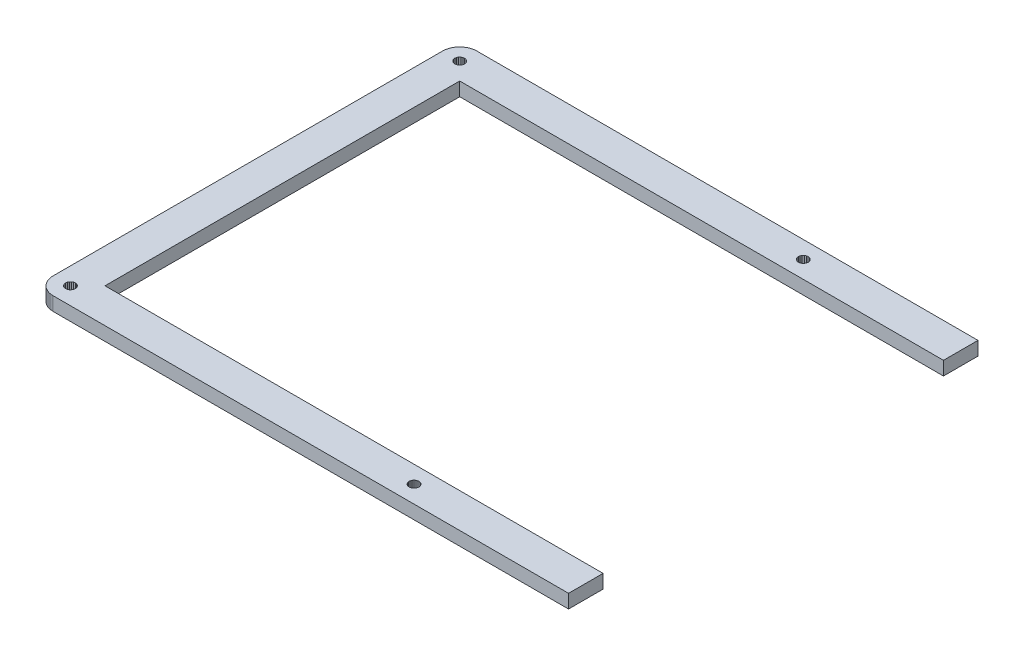
SolidWorks part; units mm, degrees
material "Copper"
ref_plane "Front Plane" through (0, 0, 0) normal (0, 0, 1) x (1, 0, 0)
ref_plane "Top Plane" through (0, 0, 0) normal (0, 1, 0) x (1, 0, 0)
ref_plane "Right Plane" through (0, 0, 0) normal (1, 0, 0) x (0, 0, -1)
sketch "Sketch1" plane through (0, 0, 0) normal (0, 1, 0) x (1, 0, 0)
  line L0 (365.806, 147.967) -> (366.279, 147.949)
  line L1 (366.279, 147.949) -> (366.748, 147.894)
  line L2 (366.748, 147.894) -> (367.21, 147.803)
  line L3 (367.21, 147.803) -> (367.661, 147.675)
  line L4 (367.661, 147.675) -> (368.106, 147.511)
  line L5 (368.106, 147.511) -> (368.533, 147.314)
  line L6 (368.533, 147.314) -> (368.942, 147.085)
  line L7 (368.942, 147.085) -> (369.334, 146.822)
  line L8 (369.334, 146.822) -> (369.704, 146.529)
  line L9 (369.704, 146.529) -> (370.05, 146.21)
  line L10 (370.05, 146.21) -> (370.371, 145.865)
  line L11 (370.371, 145.865) -> (370.664, 145.495)
  line L12 (370.664, 145.495) -> (370.925, 145.102)
  line L13 (370.925, 145.102) -> (371.154, 144.691)
  line L14 (371.154, 144.691) -> (371.352, 144.264)
  line L15 (371.352, 144.264) -> (371.514, 143.822)
  line L16 (371.514, 143.822) -> (371.641, 143.368)
  line L17 (371.641, 143.368) -> (371.733, 142.907)
  line L18 (371.733, 142.907) -> (371.789, 142.44)
  line L19 (371.789, 142.44) -> (371.807, 141.967)
  line L20 (371.807, 141.967) -> (371.807, 6.0909)
  line L21 (371.807, 6.0909) -> (371.789, 5.621)
  line L22 (371.789, 5.621) -> (371.733, 5.1539)
  line L23 (371.733, 5.1539) -> (371.641, 4.6909)
  line L24 (371.641, 4.6909) -> (371.514, 4.2375)
  line L25 (371.514, 4.2375) -> (371.352, 3.7951)
  line L26 (371.352, 3.7951) -> (371.154, 3.3679)
  line L27 (371.154, 3.3679) -> (370.925, 2.9573)
  line L28 (370.925, 2.9573) -> (370.664, 2.5645)
  line L29 (370.664, 2.5645) -> (370.371, 2.1966)
  line L30 (370.371, 2.1966) -> (370.05, 1.8493)
  line L31 (370.05, 1.8493) -> (369.704, 1.5296)
  line L32 (369.704, 1.5296) -> (369.334, 1.2375)
  line L33 (369.334, 1.2375) -> (368.942, 0.9757)
  line L34 (368.942, 0.9757) -> (368.533, 0.7455)
  line L35 (368.533, 0.7455) -> (368.106, 0.5498)
  line L36 (368.106, 0.5498) -> (367.661, 0.3859)
  line L37 (367.661, 0.3859) -> (367.21, 0.2577)
  line L38 (367.21, 0.2577) -> (366.748, 0.1654)
  line L39 (366.748, 0.1654) -> (366.279, 0.1102)
  line L40 (366.279, 0.1102) -> (365.806, 0.091)
  line L41 (365.806, 0.091) -> (6.095, 0.091)
  line L42 (6.095, 0.091) -> (5.6238, 0.1102)
  line L43 (5.6238, 0.1102) -> (5.1553, 0.1654)
  line L44 (5.1553, 0.1654) -> (4.6936, 0.2577)
  line L45 (4.6936, 0.2577) -> (4.2402, 0.3859)
  line L46 (4.2402, 0.3859) -> (3.7979, 0.5498)
  line L47 (3.7979, 0.5498) -> (3.3707, 0.7455)
  line L48 (3.3707, 0.7455) -> (2.96, 0.9757)
  line L49 (2.96, 0.9757) -> (2.5673, 1.2375)
  line L50 (2.5673, 1.2375) -> (2.198, 1.5296)
  line L51 (2.198, 1.5296) -> (1.8521, 1.8493)
  line L52 (1.8521, 1.8493) -> (1.5324, 2.1966)
  line L53 (1.5324, 2.1966) -> (1.2402, 2.5645)
  line L54 (1.2402, 2.5645) -> (0.9784, 2.9573)
  line L55 (0.9784, 2.9573) -> (0.7483, 3.3679)
  line L56 (0.7483, 3.3679) -> (0.5512, 3.7951)
  line L57 (0.5512, 3.7951) -> (0.3872, 4.2375)
  line L58 (0.3872, 4.2375) -> (0.2591, 4.6909)
  line L59 (0.2591, 4.6909) -> (0.1681, 5.1539)
  line L60 (0.1681, 5.1539) -> (0.113, 5.621)
  line L61 (0.113, 5.621) -> (0.0937, 6.0923)
  line L62 (0.0937, 6.0923) -> (0.0951, 141.967)
  line L63 (0.0951, 141.967) -> (0.113, 142.44)
  line L64 (0.113, 142.44) -> (0.1681, 142.907)
  line L65 (0.1681, 142.907) -> (0.2591, 143.368)
  line L66 (0.2591, 143.368) -> (0.3872, 143.822)
  line L67 (0.3872, 143.822) -> (0.5512, 144.264)
  line L68 (0.5512, 144.264) -> (0.7483, 144.691)
  line L69 (0.7483, 144.691) -> (0.9784, 145.102)
  line L70 (0.9784, 145.102) -> (1.2402, 145.495)
  line L71 (1.2402, 145.495) -> (1.5324, 145.865)
  line L72 (1.5324, 145.865) -> (1.8521, 146.21)
  line L73 (1.8521, 146.21) -> (2.198, 146.529)
  line L74 (2.198, 146.529) -> (2.5673, 146.822)
  line L75 (2.5673, 146.822) -> (2.96, 147.085)
  line L76 (2.96, 147.085) -> (3.3707, 147.314)
  line L77 (3.3707, 147.314) -> (3.7979, 147.511)
  line L78 (3.7979, 147.511) -> (4.2402, 147.675)
  line L79 (4.2402, 147.675) -> (4.6936, 147.803)
  line L80 (4.6936, 147.803) -> (5.1553, 147.894)
  line L81 (5.1553, 147.894) -> (5.6238, 147.949)
  line L82 (5.6238, 147.949) -> (6.095, 147.968)
  line L83 (6.095, 147.968) -> (365.806, 147.967)
  line L84 (365.252, 7.757) -> (364.769, 7.5117)
  line L85 (364.769, 7.5117) -> (364.388, 7.13)
  line L86 (364.388, 7.13) -> (364.141, 6.6504)
  line L87 (364.141, 6.6504) -> (364.06, 6.1157)
  line L88 (364.06, 6.1157) -> (364.141, 5.5838)
  line L89 (364.141, 5.5838) -> (364.388, 5.1029)
  line L90 (364.388, 5.1029) -> (364.769, 4.7211)
  line L91 (364.769, 4.7211) -> (365.252, 4.4759)
  line L92 (365.252, 4.4759) -> (365.781, 4.3918)
  line L93 (365.781, 4.3918) -> (366.317, 4.4759)
  line L94 (366.317, 4.4759) -> (366.797, 4.7211)
  line L95 (366.797, 4.7211) -> (367.178, 5.1029)
  line L96 (367.178, 5.1029) -> (367.425, 5.5838)
  line L97 (367.425, 5.5838) -> (367.506, 6.1157)
  line L98 (367.506, 6.1157) -> (367.425, 6.6504)
  line L99 (367.425, 6.6504) -> (367.178, 7.13)
  line L100 (367.178, 7.13) -> (366.797, 7.5117)
  line L101 (366.797, 7.5117) -> (366.317, 7.757)
  line L102 (366.317, 7.757) -> (365.781, 7.8411)
  line L103 (365.781, 7.8411) -> (365.252, 7.757)
  line L104 (245.361, 7.757) -> (244.88, 7.5117)
  line L105 (244.88, 7.5117) -> (244.5, 7.13)
  line L106 (244.5, 7.13) -> (244.255, 6.6504)
  line L107 (244.255, 6.6504) -> (244.169, 6.1157)
  line L108 (244.169, 6.1157) -> (244.255, 5.5838)
  line L109 (244.255, 5.5838) -> (244.5, 5.1029)
  line L110 (244.5, 5.1029) -> (244.88, 4.7211)
  line L111 (244.88, 4.7211) -> (245.361, 4.4759)
  line L112 (245.361, 4.4759) -> (245.894, 4.3918)
  line L113 (245.894, 4.3918) -> (246.428, 4.4759)
  line L114 (246.428, 4.4759) -> (246.908, 4.7211)
  line L115 (246.908, 4.7211) -> (247.29, 5.1029)
  line L116 (247.29, 5.1029) -> (247.536, 5.5838)
  line L117 (247.536, 5.5838) -> (247.62, 6.1157)
  line L118 (247.62, 6.1157) -> (247.536, 6.6504)
  line L119 (247.536, 6.6504) -> (247.29, 7.13)
  line L120 (247.29, 7.13) -> (246.908, 7.5117)
  line L121 (246.908, 7.5117) -> (246.428, 7.757)
  line L122 (246.428, 7.757) -> (245.894, 7.8411)
  line L123 (245.894, 7.8411) -> (245.361, 7.757)
  line L124 (125.473, 7.757) -> (124.992, 7.5117)
  line L125 (124.992, 7.5117) -> (124.612, 7.13)
  line L126 (124.612, 7.13) -> (124.365, 6.6504)
  line L127 (124.365, 6.6504) -> (124.281, 6.1157)
  line L128 (124.281, 6.1157) -> (124.365, 5.5838)
  line L129 (124.365, 5.5838) -> (124.612, 5.1029)
  line L130 (124.612, 5.1029) -> (124.992, 4.7211)
  line L131 (124.992, 4.7211) -> (125.473, 4.4759)
  line L132 (125.473, 4.4759) -> (126.007, 4.3918)
  line L133 (126.007, 4.3918) -> (126.54, 4.4759)
  line L134 (126.54, 4.4759) -> (127.021, 4.7211)
  line L135 (127.021, 4.7211) -> (127.403, 5.1029)
  line L136 (127.403, 5.1029) -> (127.648, 5.5838)
  line L137 (127.648, 5.5838) -> (127.732, 6.1157)
  line L138 (127.732, 6.1157) -> (127.648, 6.6504)
  line L139 (127.648, 6.6504) -> (127.403, 7.13)
  line L140 (127.403, 7.13) -> (127.021, 7.5117)
  line L141 (127.021, 7.5117) -> (126.54, 7.757)
  line L142 (126.54, 7.757) -> (126.007, 7.8411)
  line L143 (126.007, 7.8411) -> (125.473, 7.757)
  line L144 (5.5852, 7.757) -> (5.1056, 7.5117)
  line L145 (5.1056, 7.5117) -> (4.7239, 7.13)
  line L146 (4.7239, 7.13) -> (4.4786, 6.6504)
  line L147 (4.4786, 6.6504) -> (4.3932, 6.1157)
  line L148 (4.3932, 6.1157) -> (4.4786, 5.5838)
  line L149 (4.4786, 5.5838) -> (4.7239, 5.1029)
  line L150 (4.7239, 5.1029) -> (5.1056, 4.7211)
  line L151 (5.1056, 4.7211) -> (5.5852, 4.4759)
  line L152 (5.5852, 4.4759) -> (6.1185, 4.3918)
  line L153 (6.1185, 4.3918) -> (6.6532, 4.4759)
  line L154 (6.6532, 4.4759) -> (7.1327, 4.7211)
  line L155 (7.1327, 4.7211) -> (7.5145, 5.1029)
  line L156 (7.5145, 5.1029) -> (7.7597, 5.5838)
  line L157 (7.7597, 5.5838) -> (7.8438, 6.1157)
  line L158 (7.8438, 6.1157) -> (7.7597, 6.6504)
  line L159 (7.7597, 6.6504) -> (7.5145, 7.13)
  line L160 (7.5145, 7.13) -> (7.1327, 7.5117)
  line L161 (7.1327, 7.5117) -> (6.6532, 7.757)
  line L162 (6.6532, 7.757) -> (6.1185, 7.8411)
  line L163 (6.1185, 7.8411) -> (5.5852, 7.757)
  line L164 (12.1447, 135.919) -> (359.759, 135.919)
  line L165 (359.759, 135.919) -> (359.759, 12.1405)
  line L166 (359.759, 12.1405) -> (12.1447, 12.1405)
  line L167 (12.1447, 12.1405) -> (12.1447, 135.919)
  line L168 (125.473, 143.583) -> (124.992, 143.338)
  line L169 (124.992, 143.338) -> (124.612, 142.956)
  line L170 (124.612, 142.956) -> (124.365, 142.477)
  line L171 (124.365, 142.477) -> (124.281, 141.942)
  line L172 (124.281, 141.942) -> (124.365, 141.409)
  line L173 (124.365, 141.409) -> (124.612, 140.929)
  line L174 (124.612, 140.929) -> (124.992, 140.547)
  line L175 (124.992, 140.547) -> (125.473, 140.302)
  line L176 (125.473, 140.302) -> (126.007, 140.217)
  line L177 (126.007, 140.217) -> (126.54, 140.302)
  line L178 (126.54, 140.302) -> (127.021, 140.547)
  line L179 (127.021, 140.547) -> (127.403, 140.929)
  line L180 (127.403, 140.929) -> (127.648, 141.409)
  line L181 (127.648, 141.409) -> (127.732, 141.942)
  line L182 (127.732, 141.942) -> (127.648, 142.477)
  line L183 (127.648, 142.477) -> (127.403, 142.956)
  line L184 (127.403, 142.956) -> (127.021, 143.338)
  line L185 (127.021, 143.338) -> (126.54, 143.583)
  line L186 (126.54, 143.583) -> (126.007, 143.667)
  line L187 (126.007, 143.667) -> (125.473, 143.583)
  line L188 (245.361, 143.583) -> (244.88, 143.338)
  line L189 (244.88, 143.338) -> (244.5, 142.956)
  line L190 (244.5, 142.956) -> (244.255, 142.477)
  line L191 (244.255, 142.477) -> (244.169, 141.942)
  line L192 (244.169, 141.942) -> (244.255, 141.409)
  line L193 (244.255, 141.409) -> (244.5, 140.929)
  line L194 (244.5, 140.929) -> (244.88, 140.547)
  line L195 (244.88, 140.547) -> (245.361, 140.302)
  line L196 (245.361, 140.302) -> (245.894, 140.217)
  line L197 (245.894, 140.217) -> (246.428, 140.302)
  line L198 (246.428, 140.302) -> (246.908, 140.547)
  line L199 (246.908, 140.547) -> (247.29, 140.929)
  line L200 (247.29, 140.929) -> (247.536, 141.409)
  line L201 (247.536, 141.409) -> (247.62, 141.942)
  line L202 (247.62, 141.942) -> (247.536, 142.477)
  line L203 (247.536, 142.477) -> (247.29, 142.956)
  line L204 (247.29, 142.956) -> (246.908, 143.338)
  line L205 (246.908, 143.338) -> (246.428, 143.583)
  line L206 (246.428, 143.583) -> (245.894, 143.667)
  line L207 (245.894, 143.667) -> (245.361, 143.583)
  line L208 (365.252, 143.583) -> (364.769, 143.338)
  line L209 (364.769, 143.338) -> (364.388, 142.956)
  line L210 (364.388, 142.956) -> (364.141, 142.477)
  line L211 (364.141, 142.477) -> (364.06, 141.942)
  line L212 (364.06, 141.942) -> (364.141, 141.409)
  line L213 (364.141, 141.409) -> (364.388, 140.929)
  line L214 (364.388, 140.929) -> (364.769, 140.547)
  line L215 (364.769, 140.547) -> (365.252, 140.302)
  line L216 (365.252, 140.302) -> (365.781, 140.217)
  line L217 (365.781, 140.217) -> (366.317, 140.302)
  line L218 (366.317, 140.302) -> (366.797, 140.547)
  line L219 (366.797, 140.547) -> (367.178, 140.929)
  line L220 (367.178, 140.929) -> (367.425, 141.409)
  line L221 (367.425, 141.409) -> (367.506, 141.942)
  line L222 (367.506, 141.942) -> (367.425, 142.477)
  line L223 (367.425, 142.477) -> (367.178, 142.956)
  line L224 (367.178, 142.956) -> (366.797, 143.338)
  line L225 (366.797, 143.338) -> (366.317, 143.583)
  line L226 (366.317, 143.583) -> (365.781, 143.667)
  line L227 (365.781, 143.667) -> (365.252, 143.583)
  line L228 (5.5852, 143.583) -> (5.1056, 143.338)
  line L229 (5.1056, 143.338) -> (4.7239, 142.956)
  line L230 (4.7239, 142.956) -> (4.4786, 142.477)
  line L231 (4.4786, 142.477) -> (4.3932, 141.942)
  line L232 (4.3932, 141.942) -> (4.4786, 141.409)
  line L233 (4.4786, 141.409) -> (4.7239, 140.929)
  line L234 (4.7239, 140.929) -> (5.1056, 140.547)
  line L235 (5.1056, 140.547) -> (5.5852, 140.302)
  line L236 (5.5852, 140.302) -> (6.1185, 140.217)
  line L237 (6.1185, 140.217) -> (6.6532, 140.302)
  line L238 (6.6532, 140.302) -> (7.1327, 140.547)
  line L239 (7.1327, 140.547) -> (7.5145, 140.929)
  line L240 (7.5145, 140.929) -> (7.7597, 141.409)
  line L241 (7.7597, 141.409) -> (7.8438, 141.942)
  line L242 (7.8438, 141.942) -> (7.7597, 142.477)
  line L243 (7.7597, 142.477) -> (7.5145, 142.956)
  line L244 (7.5145, 142.956) -> (7.1327, 143.338)
  line L245 (7.1327, 143.338) -> (6.6532, 143.583)
  line L246 (6.6532, 143.583) -> (6.1185, 143.667)
  line L247 (6.1185, 143.667) -> (5.5852, 143.583)
  line L248 (185.9505, 147.9675) -> (185.9505, 0.091)
extrude "Boss-Extrude2" add sketch "Sketch1" along normal blind 4.7625 contours L248 L83 L82 L81 L80 L79 L78 L77 L76 L75 L74 L73 L72 L71 L70 L69 L68 L67 L66 L65 L64 L63 L62 L61 L60 L59 L58 L57 L56 L55 L54 L53 L52 L51 L50 L49 L48 L47 L46 L45 L44 L43 L42 L41 L166 L167 L164 L247 L246
sketch "Sketch2" plane through (0, 4.7625, 0) normal (0, 1, 0) x (1, 0, 0)
  line L1 (185.9505, 147.9675) -> (185.9505, 135.919) construction
  line L2 (12.1447, 135.919) -> (185.9505, 135.919) construction
  line L4 (180.9505, 141.9433) -> (180.9505, 147.9675)
  line L5 (180.9505, 147.9675) -> (185.9505, 147.9675)
  line L6 (185.9505, 141.9433) -> (185.9505, 147.9675)
  line L8 (185.9505, 141.9433) -> (185.9505, 135.919)
  line L9 (185.9505, 135.919) -> (180.9505, 135.919)
  line L10 (180.9505, 141.9433) -> (180.9505, 135.919)
extrude "Cut-Extrude2" cut sketch "Sketch2" against normal blind 4.7625
sketch "Sketch3" plane through (0, 0, -147.9675) normal (0, 0, 1) x (1, 0, 0)
  line L1 (180.9505, 0) -> (185.9505, 0)
  line L2 (180.9505, 0) -> (180.9505, 4.7625)
  line L3 (180.9505, 4.7625) -> (185.9505, 4.7625)
  line L4 (185.9505, 0) -> (185.9505, 4.7625)
extrude "Cut-Extrude3" cut sketch "Sketch3" against normal blind 4.7625
